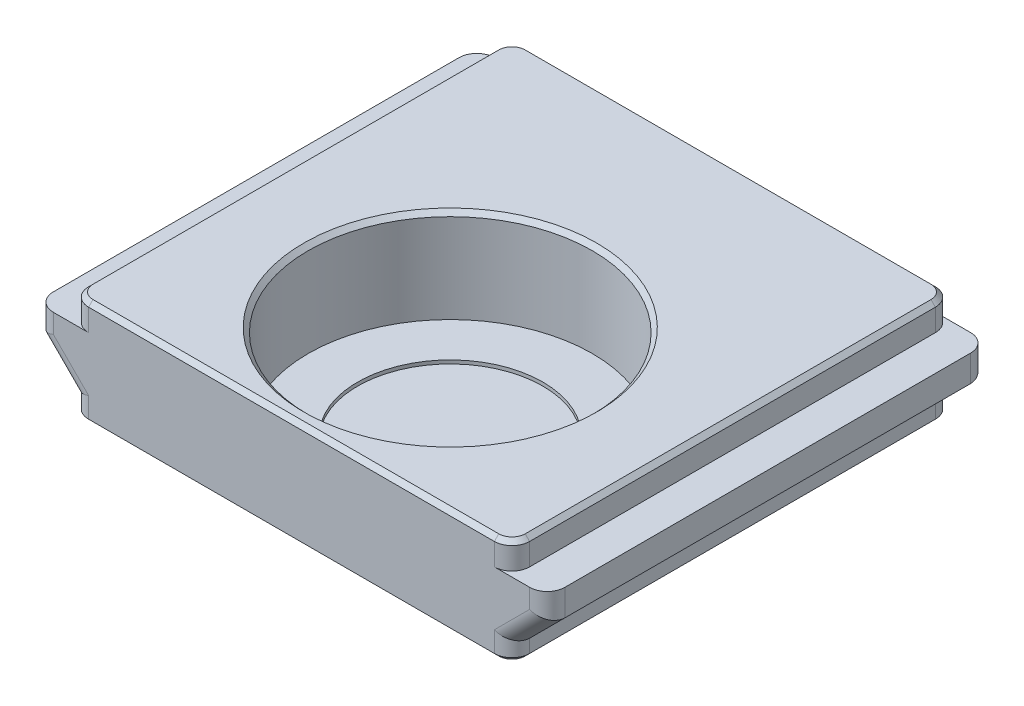
SolidWorks part; units mm, degrees
ref_plane "Front Plane" through (0, 0, 0) normal (0, 0, 1) x (1, 0, 0)
ref_plane "Top Plane" through (0, 0, 0) normal (0, 1, 0) x (1, 0, 0)
ref_plane "Right Plane" through (0, 0, 0) normal (1, 0, 0) x (0, 0, -1)
sketch "Sketch1" plane through (0, 0, 0) normal (0, 1, 0) x (1, 0, 0)
  line L1 (-12.5, -12.5) -> (12.5, -12.5)
  line L2 (-12.5, -12.5) -> (-12.5, 12.5)
  line L3 (-12.5, 12.5) -> (12.5, 12.5)
  line L4 (12.5, -12.5) -> (12.5, 12.5)
  line L5 (-12.5, -12.5) -> (12.5, 12.5) construction
  line L6 (-12.5, 12.5) -> (12.5, -12.5) construction
  point P0 (0, 0)
  dimension "D1" = 25
  dimension "D2" = 25
extrude "Boss-Extrude1" add sketch "Sketch1" along normal blind 6
sketch "Sketch2" plane through (0, 6, 0) normal (0, 1, 0) x (1, 0, 0)
  line L0 (0, -3.5) -> (0, -12.5) construction
  line L1 (-12.5, -12.5) -> (12.5, -12.5) construction
  circle A0 centre (0, -3.5) radius 8.05
  dimension "D1" = 16.1
  dimension "D2" = 9
extrude "Cut-Extrude1" cut sketch "Sketch2" against normal blind 5.5
sketch "Sketch4" plane through (0, 0, 12.5) normal (0, 0, 1) x (1, 0, 0)
  line L0 (0, 0) -> (0, 6) construction
  line L1 (-12.5, 6) -> (12.5, 6) construction
  line L2 (0, 3) -> (19.1176, 3) construction
  line L3 (12.5, 4.5) -> (14.5, 4.5)
  line L4 (12.5, 6) -> (12.5, 0) construction
  line L5 (14.5, 4.5) -> (14.5, 3)
  line L6 (14.5, 3) -> (12.5, 1)
  line L7 (12.5, 1) -> (12.5, 4.5)
  line L9 (-12.5, 1) -> (-12.5, 4.5)
  line L10 (-14.5, 3) -> (-12.5, 1)
  line L11 (-14.5, 4.5) -> (-14.5, 3)
  line L12 (-12.5, 4.5) -> (-14.5, 4.5)
  line L13 (-12.5, 0) -> (12.5, 0) construction
  dimension "D1" = 1.5
  dimension "D2" = 1
  dimension "D3" = 45
  dimension "D4" = 2
extrude "Boss-Extrude2" add sketch "Sketch4" against normal up to surface (25 mm away) up to face at (0, 3, -12.5)
sketch "Sketch5" plane through (0, 0, -12.5) normal (0, 0, -1) x (-1, 0, 0)
  line L0 (0, 0) -> (0, 6) construction
  line L1 (-12.5, 6) -> (12.5, 6) construction
  circle A0 centre (0, 3) radius 2.2
  dimension "D1" = 4.4
extrude "Cut-Extrude3" cut sketch "Sketch5" against normal blind 7.5
sketch "Sketch6" plane through (0, 0.5, 0) normal (0, 1, 0) x (1, 0, 0)
  circle A0 centre (0, -3.5) radius 5.25
  circle A1 centre (0, -3.5) radius 8.05
  circle A2 centre (0, -3.5) radius 8.05 construction
  dimension "D1" = 10.5
extrude "Boss-Extrude3" add sketch "Sketch6" along normal blind 0.2
fillet "Fillet1" radius 1 16 edges at (-13.5, 2, -12.5) (-13.5, 2, 12.5) (13.5, 2, -12.5) (13.5, 2, 12.5) (12.5, 0.5, 12.5) (14.5, 3.75, -12.5) (14.5, 3.75, 12.5) (-14.5, 3.75, -12.5) (-14.5, 3.75, 12.5) (-12.5, 0.5, 12.5) (-12.5, 0.5, -12.5) (12.5, 5.25, 12.5) (-12.5, 5.25, 12.5) (-12.5, 5.25, -12.5) (12.5, 0.5, -12.5) (12.5, 5.25, -12.5)
chamfer "Chamfer1" distance 0.5 angle 45 1 edges at (-2.2, 3, -12.5)
chamfer "Chamfer2" distance 0.25 angle 45 17 edges at (0, 0, -12.5) (-12.5, 0, 0) (0, 0, 12.5) (12.5, 0, 0) (0, 6, 12.5) (-12.5, 6, 0) (0, 6, -12.5) (12.5, 6, 0) (0, 6, 11.55) (12.2071, 0, -12.2071) (-12.2071, 0, -12.2071) (-12.2071, 0, 12.2071) (12.2071, 0, 12.2071) (-12.2071, 6, 12.2071) (-12.2071, 6, -12.2071) (12.2071, 6, -12.2071) (12.2071, 6, 12.2071)
